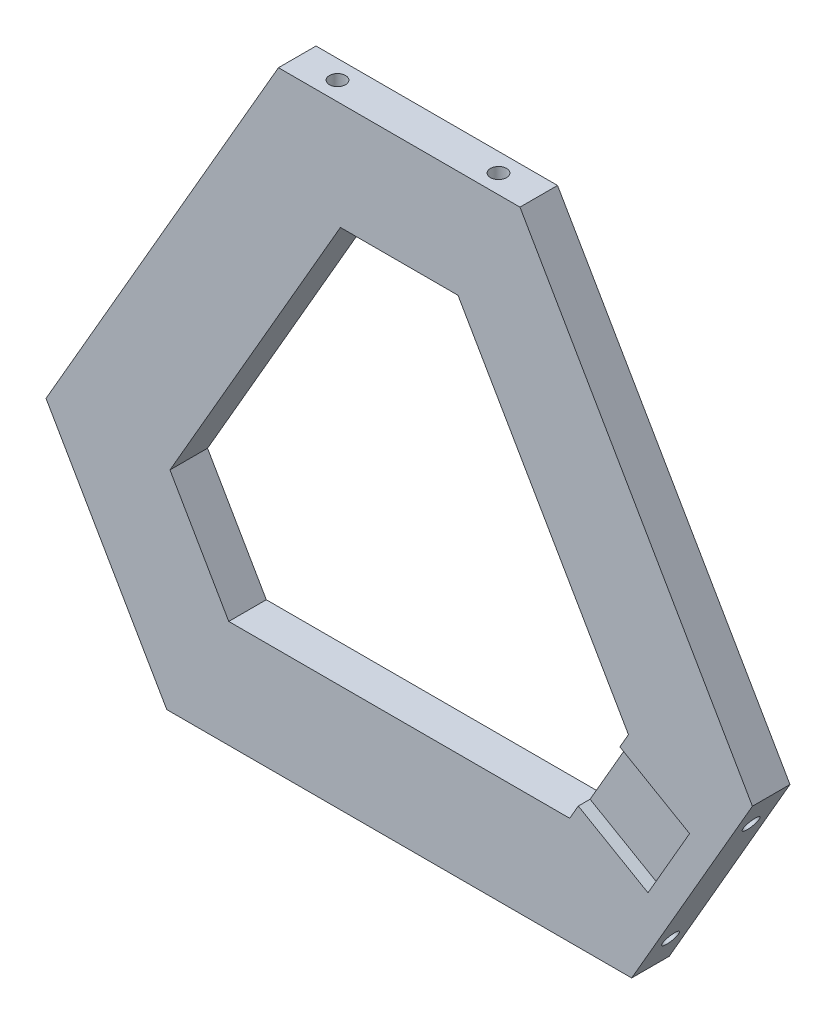
SolidWorks part; units mm, degrees
ref_plane "前基準面" through (0, 0, 0) normal (0, 0, 1) x (1, 0, 0)
ref_plane "上基準面" through (0, 0, 0) normal (0, 1, 0) x (1, 0, 0)
ref_plane "右基準面" through (0, 0, 0) normal (1, 0, 0) x (0, 0, -1)
sketch "草圖1" plane through (0, 0, 0) normal (0, 0, 1) x (1, 0, 0)
  line L0 (0, 0) -> (0, 63) construction
  line L1 (0, 0) -> (54.5596, -31.5) construction
  line L2 (0, 0) -> (-54.5596, -31.5) construction
  line L3 (-22.5, 63) -> (22.5, 63)
  line L4 (65.8096, -12.0144) -> (43.3096, -50.9856)
  line L5 (-43.3096, -50.9856) -> (-65.8096, -12.0144)
  line L6 (-65.8096, -12.0144) -> (-22.5, 63)
  line L7 (22.5, 63) -> (65.8096, -12.0144)
  line L8 (43.3096, -50.9856) -> (-43.3096, -50.9856)
  point P6 (0, 0)
  point P15 (0, 0)
  dimension "D1" = 3
  dimension "D2" = 63
  dimension "D3" = 45
  dimension "D5" = 3
extrude "填料-伸長1" add sketch "草圖1" along normal blind 7
sketch "草圖11" plane through (0, 0, 7) normal (0, 0, 1) x (1, 0, 0)
  line L0 (0, 0) -> (0, 63) construction
  line L1 (22.5, 63) -> (-22.5, 63) construction
  line L2 (0, 0) -> (54.5596, -31.5) construction
  line L3 (43.3096, -50.9856) -> (65.8096, -12.0144) construction
  line L4 (0, 0) -> (0, -50.9856) construction
  line L5 (-43.3096, -50.9856) -> (43.3096, -50.9856) construction
sketch "草圖12" plane through (-54.5596, -31.5, 0) normal (-0.866, -0.5, 0) x (0, 0, 1)
  line L0 (3.5, 22.5) -> (3.5, -22.5) construction
  line L1 (7, 22.5) -> (0, 22.5) construction
  line L2 (7, -22.5) -> (0, -22.5) construction
  line L3 (0, 0) -> (7.5853, 0) construction
  line L5 (-105.0534, 64.6667) -> (-114.7835, 70.2528) construction
  line L6 (-114.7835, 70.2528) -> (-119.9358, 70.2528) construction
  circle A0 centre (3.5, 15) radius 1.5
  circle A1 centre (3.5, -15) radius 1.5
  dimension "D1" = 3
  dimension "D2" = 15
extrude "除料-伸長1" cut sketch "草圖12" against normal blind 12
sketch "草圖13" plane through (54.5596, -31.5, 0) normal (0.866, -0.5, 0) x (0, 0, -1)
  line L0 (-3.5, 22.5) -> (-3.5, -22.5) construction
  line L1 (-7, 22.5) -> (0, 22.5) construction
  line L2 (-7, -22.5) -> (0, -22.5) construction
  line L3 (-7, 0) -> (0, 0) construction
  line L4 (-7, 0) -> (-7, -44.1548) construction
  circle A0 centre (-3.5, 15) radius 1.5
  circle A1 centre (-3.5, -15) radius 1.5
  dimension "D1" = 3
  dimension "D2" = 15
extrude "除料-伸長2" cut sketch "草圖13" against normal blind 12
sketch "草圖14" plane through (0, 63, 0) normal (0, 1, 0) x (1, 0, 0)
  line L0 (-22.5, -3.5) -> (22.5, -3.5) construction
  line L1 (-22.5, -7) -> (-22.5, 0) construction
  line L2 (22.5, -7) -> (22.5, 0) construction
  line L3 (0, 0) -> (0, -7) construction
  line L4 (0, -7) -> (54.5596, -7) construction
  circle A0 centre (-15, -3.5) radius 1.5
  circle A1 centre (15, -3.5) radius 1.5
  dimension "D1" = 3
  dimension "D2" = 15
extrude "除料-伸長3" cut sketch "草圖14" against normal blind 12
sketch "草圖15" plane through (0, 0, 7) normal (0, 0, 1) x (1, 0, 0)
  line L0 (10.953, 43) -> (-10.953, 43)
  line L1 (-10.953, 43) -> (-42.7156, -12.0144)
  line L2 (-42.7156, -12.0144) -> (-31.7626, -30.9856)
  line L3 (-31.7626, -30.9856) -> (31.7626, -30.9856)
  line L4 (31.7626, -30.9856) -> (42.7156, -12.0144)
  line L5 (42.7156, -12.0144) -> (10.953, 43)
  line L6 (22.5, 63) -> (-22.5, 63)
  line L7 (65.8096, -12.0144) -> (22.5, 63)
  line L8 (43.3096, -50.9856) -> (65.8096, -12.0144)
  line L9 (-43.3096, -50.9856) -> (43.3096, -50.9856)
  line L10 (-65.8096, -12.0144) -> (-43.3096, -50.9856)
  line L11 (-22.5, 63) -> (-65.8096, -12.0144)
  line L12 (22.5, 63) -> (-22.5, 63)
  line L13 (65.8096, -12.0144) -> (22.5, 63)
  line L14 (43.3096, -50.9856) -> (65.8096, -12.0144)
  line L15 (-43.3096, -50.9856) -> (43.3096, -50.9856)
  line L16 (-65.8096, -12.0144) -> (-43.3096, -50.9856)
  line L17 (-22.5, 63) -> (-65.8096, -12.0144)
  dimension "D1" = 0
  dimension "D2" = 20
extrude "除料-伸長4" cut sketch "草圖15" against normal through all contours L4 L5 L0 L1 L2 L3
sketch "草圖16" plane through (0, 0, 7) normal (0, 0, 1) x (1, 0, 0)
  line L0 (41.1141, -14.7883) -> (54.1045, -22.2883)
  line L1 (31.7626, -30.9856) -> (42.7156, -12.0144) construction
  line L2 (54.1045, -22.2883) -> (46.3545, -35.7117)
  line L3 (46.3545, -35.7117) -> (33.3641, -28.2117)
  line L4 (33.3641, -28.2117) -> (41.1141, -14.7883)
  line L5 (0, 0) -> (54.5596, -31.5) construction
  dimension "D1" = 15.5
  dimension "D2" = 15
  dimension "D3" = 7.75
extrude "除料-伸長5" cut sketch "草圖16" against normal blind 2.2
sketch "草圖17" plane through (0, 0, 4.8) normal (0, 0, 1) x (1, 0, 0)
  line L0 (41.1141, -14.7883) -> (39.7141, -17.2132)
  line L1 (41.1141, -14.7883) -> (33.3641, -28.2117) construction
  line L2 (39.7141, -17.2132) -> (52.7045, -24.7132)
  line L3 (41.1141, -14.7883) -> (54.1045, -22.2883)
  line L4 (54.1045, -22.2883) -> (52.7045, -24.7132)
  line L5 (46.3545, -35.7117) -> (54.1045, -22.2883) construction
  dimension "D1" = 2.8
extrude "除料-伸長6" cut sketch "草圖17" against normal through all
